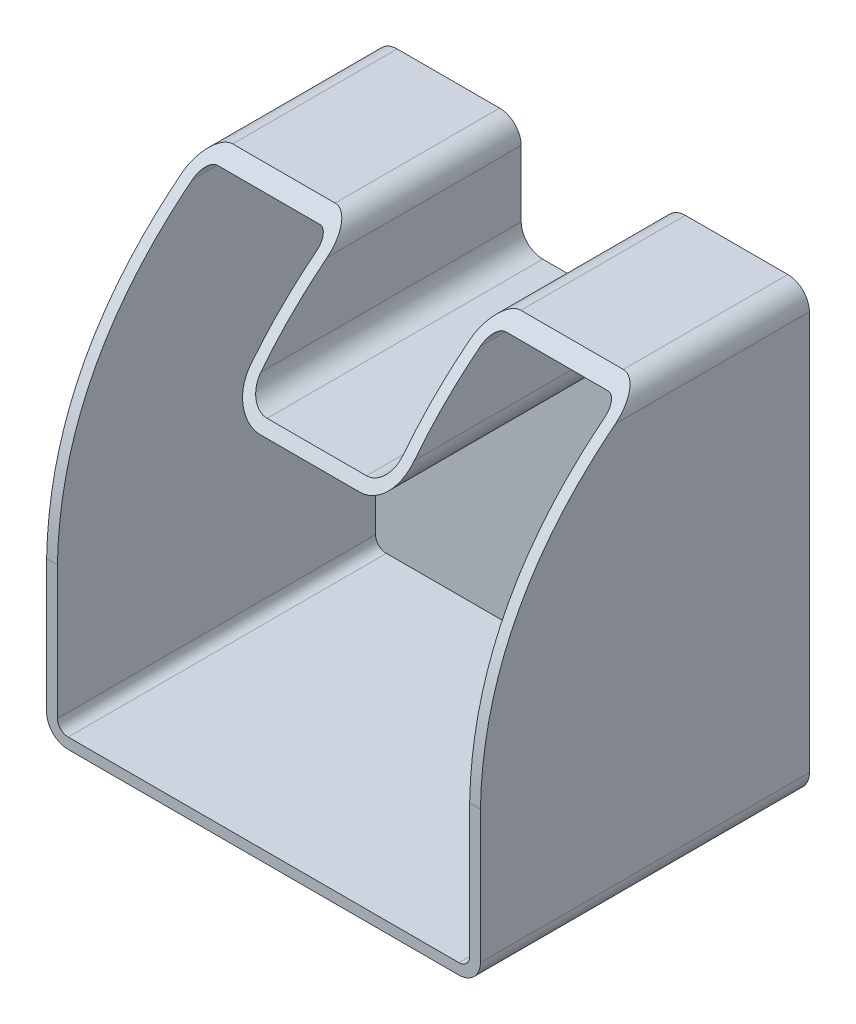
SolidWorks part; units mm, degrees
ref_plane "Front Plane" through (0, 0, 0) normal (0, 0, 1) x (1, 0, 0)
ref_plane "Top Plane" through (0, 0, 0) normal (0, 1, 0) x (1, 0, 0)
ref_plane "Right Plane" through (0, 0, 0) normal (1, 0, 0) x (0, 0, -1)
sketch "Sketch1" plane through (0, 0, 1146.7084) normal (0, 0, -1) x (-1, 0, 0)
  line L0 (399.0528, -20.3228) -> (399.0528, 53.6772) construction
  line L1 (398.0528, -24.3228) -> (325.6128, -24.3228)
  line L2 (402.0528, -20.3228) -> (402.0528, 53.6772)
  line L3 (398.0528, 57.6772) -> (379.0528, 57.6772)
  line L4 (321.6128, -20.3228) -> (321.6128, 53.6772)
  line L5 (327.6128, 8.2662) -> (327.6128, 16.5162) construction
  line L6 (367.5528, -21.3228) -> (357.6528, -21.3228) construction
  line L7 (379.0528, 54.6772) -> (398.0528, 54.6772) construction
  line L10 (378.0528, -20.3228) -> (378.0528, 53.6772) construction
  line L11 (352.6128, 37.4206) -> (371.0528, 37.4206)
  line L12 (348.6128, 41.4206) -> (348.6128, 53.6772)
  line L14 (375.0528, 41.4206) -> (375.0528, 53.6772)
  line L17 (339.2845, 34.4206) -> (345.5337, 34.4206) construction
  line L18 (344.6128, 57.6772) -> (325.6128, 57.6772)
  arc A0 (379.0528, 57.6772) -> (375.0528, 53.6772) centre (379.0528, 53.6772) ccw
  arc A1 (371.0528, 37.4206) -> (375.0528, 41.4206) centre (371.0528, 41.4206) ccw
  arc A2 (352.6128, 37.4206) -> (348.6128, 41.4206) centre (352.6128, 41.4206) cw
  arc A3 (348.6128, 53.6772) -> (344.6128, 57.6772) centre (344.6128, 53.6772) ccw
  arc A4 (398.0528, -24.3228) -> (402.0528, -20.3228) centre (398.0528, -20.3228) ccw
  arc A5 (325.6128, -24.3228) -> (321.6128, -20.3228) centre (325.6128, -20.3228) cw
  arc A6 (402.0528, 53.6772) -> (398.0528, 57.6772) centre (398.0528, 53.6772) ccw
  arc A7 (325.6128, 57.6772) -> (321.6128, 53.6772) centre (325.6128, 53.6772) ccw
  point P21 (353.0528, 37.1024)
  point P29 (348.6128, 57.6772)
  point P38 (0, 0)
  point P39 (328.375, 57.6772)
  dimension "D7" = 4
  dimension "D1" = 3
  dimension "D2" = 3
  dimension "D3" = 6
  dimension "D4" = 3
  dimension "D5" = 3
  dimension "D6" = 3
  dimension "D8" = 19
extrude "Boss-Extrude2" add sketch "Sketch1" along normal blind 10 and the other way blind 51
shell "Shell2" thickness 2
sketch "Sketch2" plane through (-321.6128, 0, 0) normal (1, 0, 0) x (0, 0, -1)
  line L0 (-1197.7084, 53.6772) -> (-1197.7084, -20.3228) construction
  line L1 (-1197.7084, 57.6772) -> (-1136.7084, 57.6772) construction
  line L2 (-1197.7084, 4.3312) -> (-1202.7005, 4.3312)
  line L3 (-1202.7005, 4.3312) -> (-1202.7005, 60.8892)
  line L4 (-1202.7005, 60.8892) -> (-1167.2084, 60.8892)
  line L5 (-1167.2084, 60.8892) -> (-1167.2084, 57.6772)
  spline S0 degree 2 poles (-1197.7084, 4.3312) (-1197.0688, 37.525) (-1167.2084, 57.6772) knots 0 0 0 1 1 1
extrude "Cut-Extrude2" cut sketch "Sketch2" against normal through all
sketch "Sketch4" plane through (0, 0, 1136.7084) normal (0, 0, -1) x (-1, 0, 0)
  line L0 (361.8328, 37.4206) -> (321.6128, 37.4206) construction
  line L1 (371.0528, 37.4206) -> (352.6128, 37.4206) construction
  line L2 (321.6128, 53.6772) -> (321.6128, -20.3228) construction
  line L3 (348.6128, 57.6772) -> (348.6128, 37.4206) construction
  line L4 (344.6128, 57.6772) -> (325.6128, 57.6772) construction
  line L5 (348.6128, 47.5489) -> (321.6128, 47.5489) construction
  circle A1 centre (335.1128, 47.5489) radius 5.05
  dimension "D1" = 10.1
extrude "Cut-Extrude3" cut sketch "Sketch4" against normal through all
